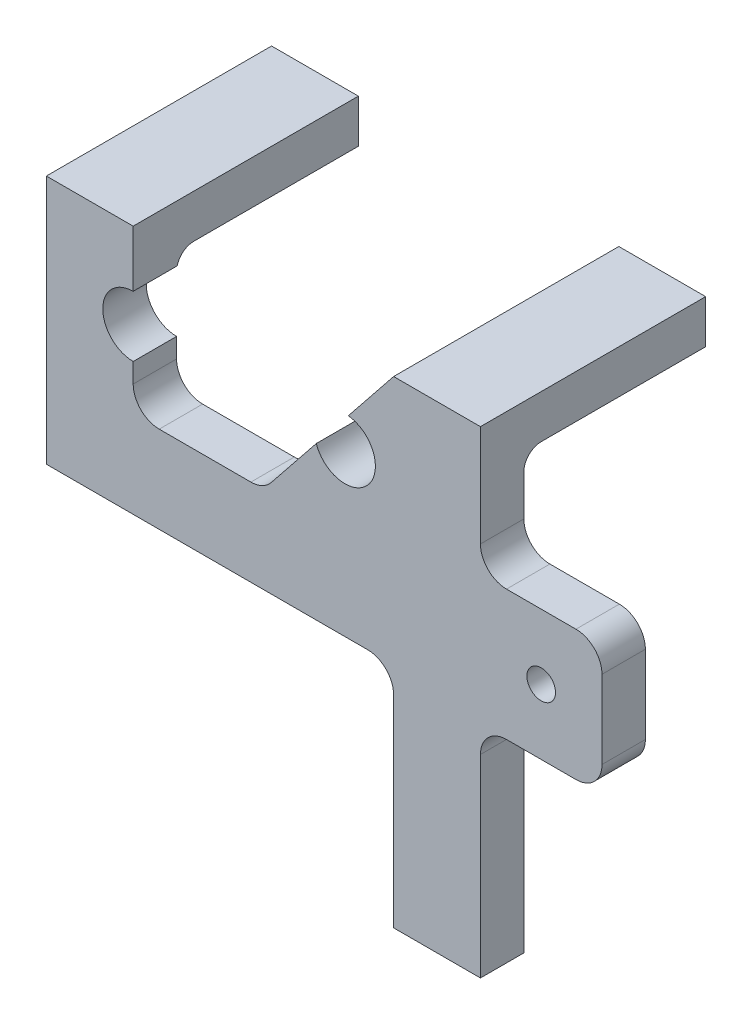
SolidWorks part; units mm, degrees
ref_plane "Front Plane" through (0, 0, 0) normal (0, 0, 1) x (1, 0, 0)
ref_plane "Top Plane" through (0, 0, 0) normal (0, 1, 0) x (1, 0, 0)
ref_plane "Right Plane" through (0, 0, 0) normal (1, 0, 0) x (0, 0, -1)
sketch "Sketch1" plane through (0, 0, 0) normal (0, 0, 1) x (1, 0, 0)
  line L0 (0, 0) -> (0, 69.85)
  line L1 (0, 69.85) -> (-12.7, 69.85)
  line L2 (-12.7, 69.85) -> (-19.3254, 61.5683)
  line L4 (-50.8, 69.85) -> (-63.5, 69.85)
  line L5 (-63.5, 69.85) -> (-63.5, 33.3375)
  line L7 (-63.5, 33.3375) -> (-12.7, 33.3375)
  line L8 (-12.7, 33.3375) -> (-12.7, 0)
  line L9 (-12.7, 0) -> (0, 0)
  line L10 (-50.8, 69.85) -> (-50.8, 61.595)
  line L11 (-50.8, 46.0375) -> (-31.75, 46.0375)
  line L12 (-24.0157, 55.7054) -> (-31.75, 46.0375)
  line L13 (-50.8, 52.705) -> (-50.8, 46.0375)
  arc A0 (-50.8, 61.595) -> (-50.8, 52.705) centre (-50.8, 57.15) ccw
  arc A1 (-24.0157, 55.7054) -> (-19.3254, 61.5683) centre (-19.812, 57.15) ccw
  dimension "D9" = 8.89
  dimension "D12" = 8.89
  dimension "D1" = 69.85
  dimension "D2" = 12.7
  dimension "D3" = 12.7
  dimension "D4" = 63.5
  dimension "D5" = 23.8125
  dimension "D6" = 19.05
  dimension "D7" = 12.7
  dimension "D8" = 12.7
  dimension "D10" = 12.7
  dimension "D11" = 30.988
extrude "Boss-Extrude1" add sketch "Sketch1" along normal blind 6.35
sketch "Sketch2" plane through (0, 0, 6.35) normal (0, 0, -1) x (-1, 0, 0)
  line L0 (63.5, 69.85) -> (63.5, 33.3375) construction
  line L1 (0, 69.85) -> (12.7, 69.85)
  line L2 (0, 69.85) -> (0, 63.5)
  line L3 (0, 63.5) -> (12.7, 63.5)
  line L4 (12.7, 69.85) -> (12.7, 63.5)
  line L5 (50.8, 69.85) -> (63.5, 69.85)
  line L6 (50.8, 69.85) -> (50.8, 63.5)
  line L7 (50.8, 63.5) -> (63.5, 63.5)
  line L8 (63.5, 69.85) -> (63.5, 63.5)
  dimension "D1" = 6.35
extrude "Boss-Extrude3" add sketch "Sketch2" along normal blind 32.9438
fillet "Fillet1" radius 2.54 3 edges at (-57.15, 63.5, 0) (-6.35, 63.5, 0) (-12.7, 66.675, 0)
sketch "Sketch3" plane through (0, 0, 6.35) normal (0, 0, 1) x (1, 0, 0)
  line L0 (0, 51.1759) -> (17.78, 51.1759)
  line L1 (0, 0) -> (0, 69.85) construction
  line L2 (17.78, 51.1759) -> (17.78, 32.1259)
  line L3 (17.78, 32.1259) -> (0, 32.1259)
  line L4 (0, 32.1259) -> (0, 51.1759)
  line L5 (0, 69.85) -> (-12.7, 69.85) construction
  line L6 (17.78, 41.6509) -> (-15.8152, 41.6509) construction
  circle A0 centre (8.89, 41.6509) radius 2.0955
  point P12 (0, 0)
  point P13 (0, 0)
  point P14 (8.89, 51.1759)
  dimension "D4" = 4.191
  dimension "D1" = 19.05
  dimension "D2" = 18.6741
  dimension "D3" = 17.78
extrude "Boss-Extrude4" add sketch "Sketch3" against normal up to surface (6.35 mm away) up to face at (-29.3193, 45.2935, 0)
fillet "Fillet2" radius 3.81 7 edges at (-50.8, 46.0375, 3.175) (-31.75, 46.0375, 3.175) (-12.7, 33.3375, 3.175) (0, 32.1259, 3.175) (0, 51.1759, 3.175) (17.78, 32.1259, 3.175) (17.78, 51.1759, 3.175)
